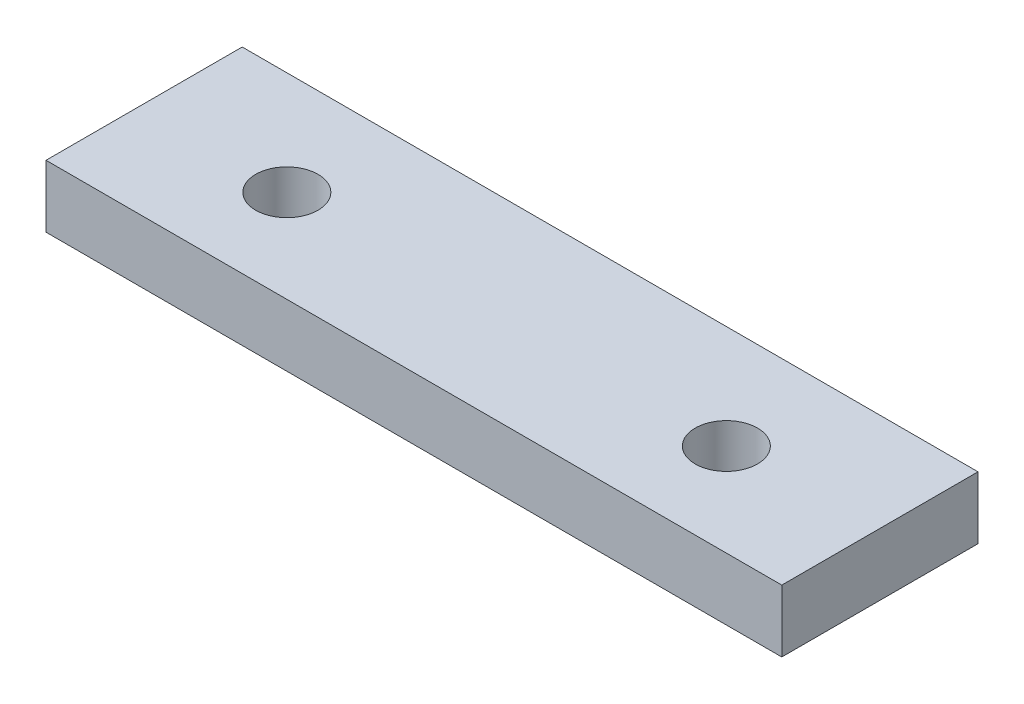
SolidWorks part; units mm, degrees
material "Plain Carbon Steel"
ref_plane "Front Plane" through (0, 0, 0) normal (0, 0, 1) x (1, 0, 0)
ref_plane "Top Plane" through (0, 0, 0) normal (0, 1, 0) x (1, 0, 0)
ref_plane "Right Plane" through (0, 0, 0) normal (1, 0, 0) x (0, 0, -1)
sketch "Sketch1" plane through (0, 0, 0) normal (1, 0, 0) x (0, 0, -1)
  line L1 (0, 0) -> (40, 0)
  line L2 (0, 0) -> (0, 12.7)
  line L3 (0, 12.7) -> (40, 12.7)
  line L4 (40, 0) -> (40, 12.7)
  dimension "D1" = 12.7
  dimension "D2" = 40
extrude "Boss-Extrude1" add sketch "Sketch1" along normal blind 150
sketch "Sketch2" plane through (0, 12.7, 0) normal (0, 1, 0) x (1, 0, 0)
  line L0 (0, 18.9) -> (30.2, 18.9) construction
  line L2 (150, 18.9) -> (119.8, 18.9) construction
  line L5 (150, 0) -> (0, 0) construction
  line L6 (0, 40) -> (0, 0) construction
  line L7 (150, 40) -> (150, 0) construction
  circle A0 centre (30.2, 18.9) radius 6.35
  circle A1 centre (119.8, 18.9) radius 6.35
  dimension "D2" = 12.7
  dimension "D4" = 12.7
  dimension "D1" = 30.2
  dimension "D3" = 30.2
  dimension "D5" = 18.9
extrude "Cut-Extrude1" cut sketch "Sketch2" against normal up to next
